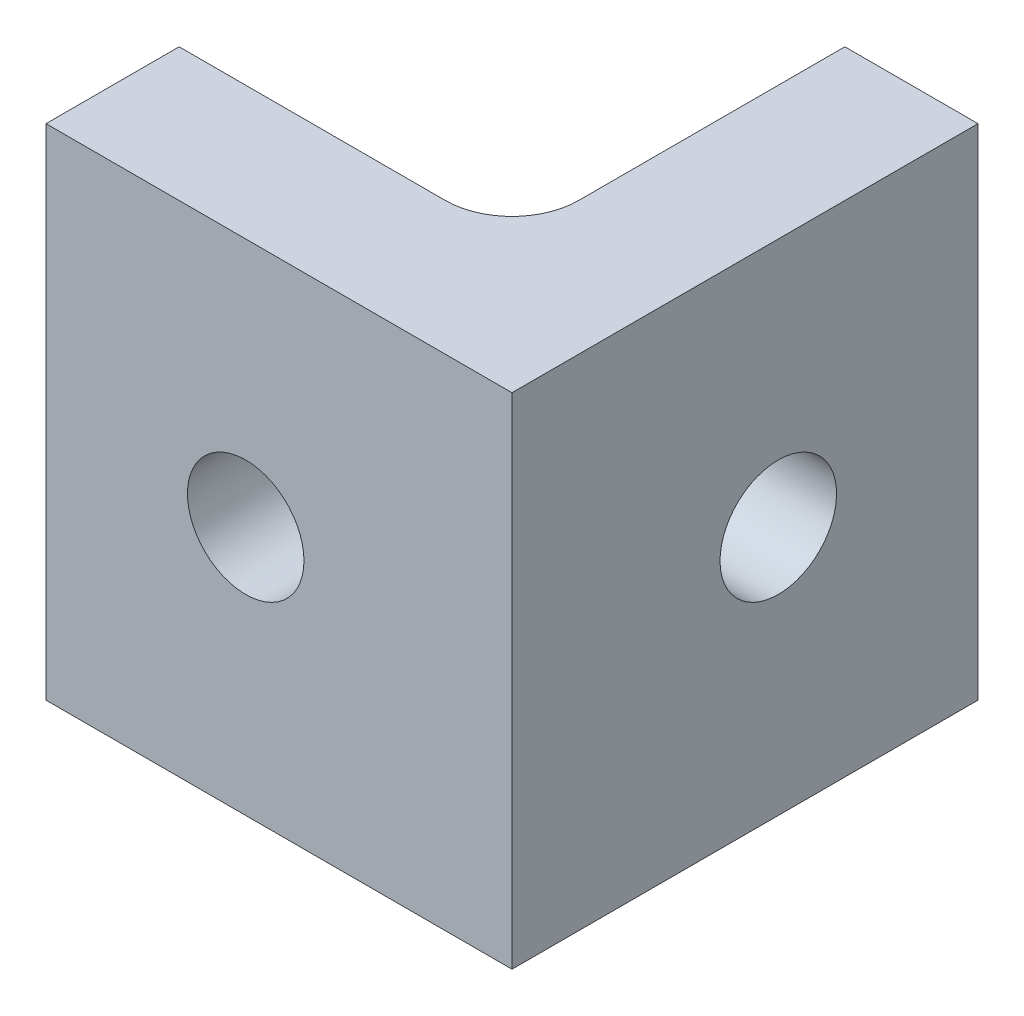
SolidWorks part; units mm, degrees
ref_plane "前视基准面" through (0, 0, 0) normal (0, 0, 1) x (1, 0, 0)
ref_plane "上视基准面" through (0, 0, 0) normal (0, 1, 0) x (1, 0, 0)
ref_plane "右视基准面" through (0, 0, 0) normal (1, 0, 0) x (0, 0, -1)
sketch "草图1" plane through (0, 0, 0) normal (0, 0, 1) x (1, 0, 0)
  line L1 (6, -7.5) -> (-6, -7.5)
  line L2 (6, -7.5) -> (6, 7.5)
  line L3 (6, 7.5) -> (-6, 7.5)
  line L4 (-6, -7.5) -> (-6, 7.5)
  line L5 (0, 7.5) -> (0, -7.5) construction
  line L6 (6, 0) -> (-6, 0) construction
  circle A0 centre (2, 0) radius 1.75
  point P0 (0, 0)
  dimension "D3" = 3.5
  dimension "D1" = 6
  dimension "D2" = 15
  dimension "D4" = 4
extrude "凸台-拉伸1" add sketch "草图1" along normal blind 4
sketch "草图2" plane through (6, 0, 0) normal (1, 0, 0) x (0, 0, -1)
  line L0 (-4, 7.5) -> (-4, -7.5)
  line L1 (-4, -7.5) -> (12, -7.5)
  line L2 (12, -7.5) -> (12, 7.5)
  line L3 (12, 7.5) -> (-4, 7.5)
  circle A0 centre (4, 0) radius 1.75
  dimension "D1" = 3.5
  dimension "D2" = 4
extrude "凸台-拉伸2" add sketch "草图2" along normal blind 4
fillet "圆角1" radius 2 1 edges at (6, 0, 0)
sketch "草图3" plane through (6, 0, 0) normal (-1, 0, 0) x (0, 0, 1)
  line L0 (-12, 7.5) -> (-12, -7.5)
  line L1 (-12, -7.5) -> (-10, -7.5)
  line L2 (-2, -7.5) -> (-12, -7.5) construction
  line L3 (-10, -7.5) -> (-10, 7.5)
  line L4 (-12, 7.5) -> (-2, 7.5) construction
  line L5 (-10, 7.5) -> (-12, 7.5)
  dimension "D1" = 2
extrude "切除-拉伸1" cut sketch "草图3" against normal blind 4
sketch "草图4" plane through (0, 0, 0) normal (0, 0, -1) x (-1, 0, 0)
  line L0 (6, 7.5) -> (4, 7.5)
  line L1 (-4, 7.5) -> (6, 7.5) construction
  line L2 (4, 7.5) -> (4, -7.5)
  line L3 (6, -7.5) -> (-4, -7.5) construction
  line L4 (4, -7.5) -> (6, -7.5)
  line L5 (6, -7.5) -> (6, 7.5)
  dimension "D1" = 2
extrude "切除-拉伸2" cut sketch "草图4" against normal blind 4
